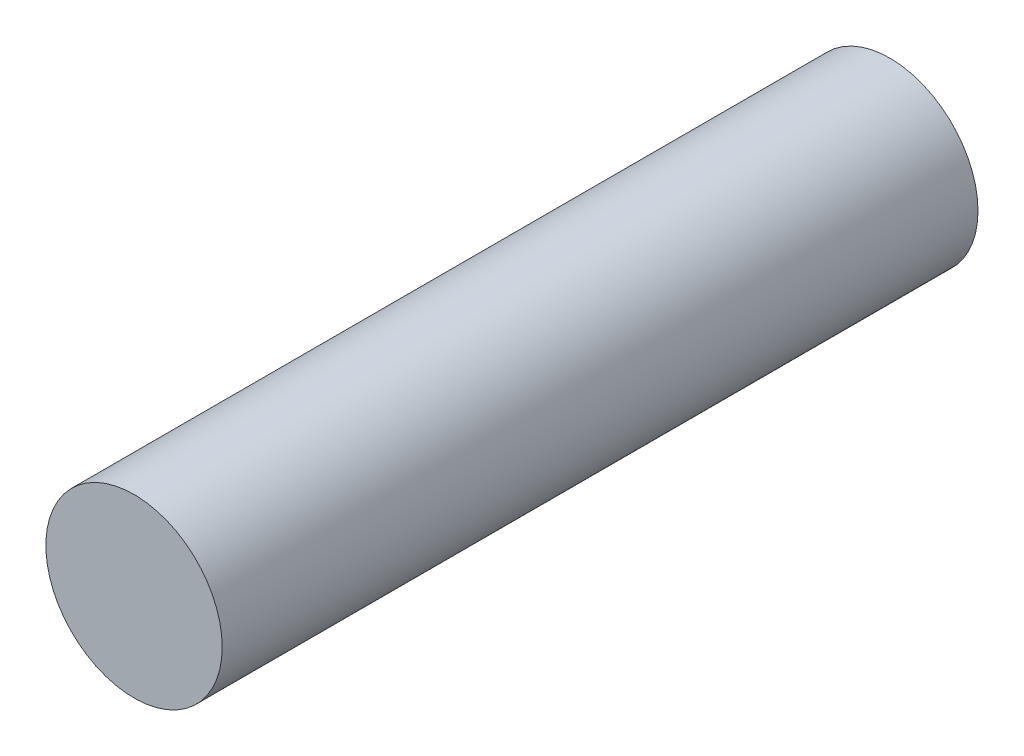
SolidWorks part; units mm, degrees
ref_plane "Front Plane" through (0, 0, 0) normal (0, 0, 1) x (1, 0, 0)
ref_plane "Top Plane" through (0, 0, 0) normal (0, 1, 0) x (1, 0, 0)
ref_plane "Right Plane" through (0, 0, 0) normal (1, 0, 0) x (0, 0, -1)
sketch "Sketch1" plane through (0, 0, 0) normal (0, 0, 1) x (1, 0, 0)
  line L0 (0, 0) -> (8.6101, 0) construction
  line L1 (0, 0) -> (0, 20.7) construction
  circle A0 centre (0, 20.7) radius 3.5
  dimension "D2" = 7
  dimension "D1" = 20.7
extrude "Boss-Extrude1" add sketch "Sketch1" along normal blind 30
